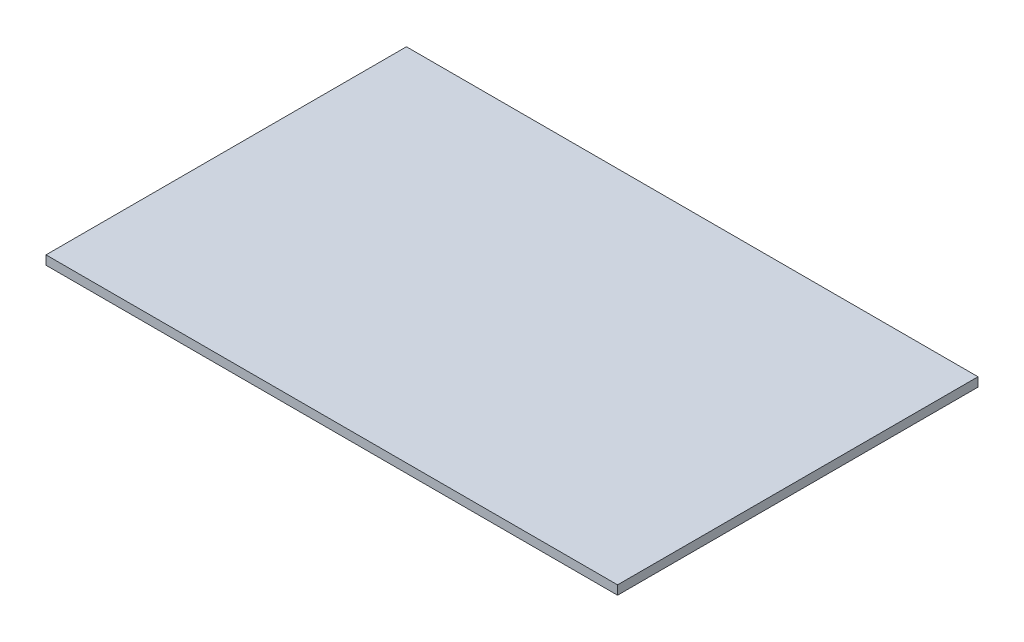
SolidWorks part; units mm, degrees
ref_plane "Front Plane" through (0, 0, 0) normal (0, 0, 1) x (1, 0, 0)
ref_plane "Top Plane" through (0, 0, 0) normal (0, 1, 0) x (1, 0, 0)
ref_plane "Right Plane" through (0, 0, 0) normal (1, 0, 0) x (0, 0, -1)
sketch "Sketch1" plane through (0, 0, 0) normal (0, 1, 0) x (1, 0, 0)
  line L1 (42.8, -26.99) -> (-42.8, -26.99)
  line L2 (42.8, -26.99) -> (42.8, 26.99)
  line L3 (42.8, 26.99) -> (-42.8, 26.99)
  line L4 (-42.8, -26.99) -> (-42.8, 26.99)
  line L5 (42.8, -26.99) -> (-42.8, 26.99) construction
  line L6 (42.8, 26.99) -> (-42.8, -26.99) construction
  point P0 (0, 0)
  dimension "D1" = 85.6
  dimension "D2" = 53.98
extrude "Boss-Extrude1" add sketch "Sketch1" along normal blind 1.35
